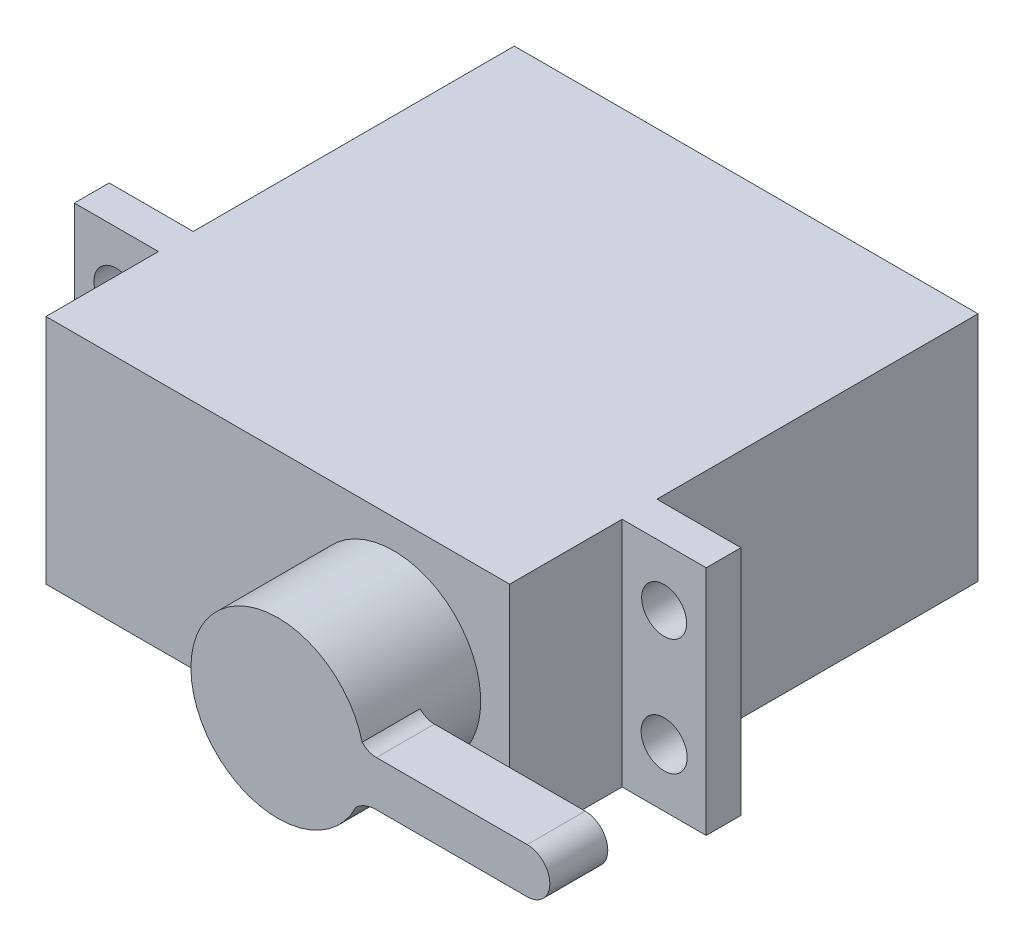
SolidWorks part; units mm, degrees
ref_plane "Front Plane" through (0, 0, 0) normal (0, 0, 1) x (1, 0, 0)
ref_plane "Top Plane" through (0, 0, 0) normal (0, 1, 0) x (1, 0, 0)
ref_plane "Right Plane" through (0, 0, 0) normal (1, 0, 0) x (0, 0, -1)
sketch "Sketch1" plane through (0, 0, 0) normal (0, 1, 0) x (1, 0, 0)
  line L1 (-27.6845, 15.2601) -> (12.3155, 15.2601)
  line L2 (-27.6845, 15.2601) -> (-27.6845, -25.1399)
  line L3 (-27.6845, -25.1399) -> (12.3155, -25.1399)
  line L4 (12.3155, 15.2601) -> (12.3155, -25.1399)
  dimension "D1" = 40
  dimension "D2" = 40.4
extrude "Boss-Extrude1" add sketch "Sketch1" along normal blind 20
sketch "Sketch3" plane through (12.3155, 0, 0) normal (1, 0, 0) x (0, 0, -1)
  line L0 (-25.1399, 20) -> (15.2601, 20) construction
  line L1 (-25.1399, 0) -> (15.2601, 0) construction
  line L2 (-15.4399, 20) -> (-12.4399, 20)
  line L3 (-15.4399, 20) -> (-15.4399, 0)
  line L4 (-15.4399, 0) -> (-12.4399, 0)
  line L5 (-12.4399, 20) -> (-12.4399, 0)
  line L7 (15.2601, 20) -> (15.2601, 0) construction
  dimension "D1" = 27.7
  dimension "D2" = 3
extrude "Boss-Extrude2" add sketch "Sketch3" along normal blind 7.25
sketch "Sketch4" plane through (0, 0, 0) normal (0, -1, 0) x (-1, 0, 0)
  line L0 (7.6845, -25.1399) -> (7.6845, 15.2601) construction
  line L1 (27.6845, -25.1399) -> (-12.3155, -25.1399) construction
  line L2 (-12.3155, 15.2601) -> (27.6845, 15.2601) construction
ref_plane "Plane1" through (-7.6845, 0, 0) normal (-1, 0, 0) x (0, 0, 1)
mirror "Mirror1" about plane through (-7.6845, 0, 0) normal (-1, 0, 0) of "Boss-Extrude2"
sketch "Sketch5" plane through (0, 0, 15.4399) normal (0, 0, 1) x (1, 0, 0)
  line L1 (19.5655, 0) -> (12.3155, 0) construction
  circle A0 centre (15.9405, 15) radius 1.9389
  circle A1 centre (15.9405, 5) radius 1.9865
  dimension "D1" = 10
  dimension "D3" = 5
extrude "Cut-Extrude1" cut sketch "Sketch5" against normal blind 7.25
mirror "Mirror2" about plane through (-7.6845, 0, 0) normal (-1, 0, 0) of "Cut-Extrude1"
sketch "Sketch6" plane through (0, 0, 25.1399) normal (0, 0, 1) x (1, 0, 0)
  line L0 (-27.6845, 20) -> (-27.6845, 0) construction
  circle A0 centre (2.3155, 10) radius 7.5
  dimension "D1" = 15
  dimension "D2" = 30
extrude "Boss-Extrude3" add sketch "Sketch6" along normal blind 10
sketch "Sketch8" plane through (0, 0, 35.1399) normal (0, 0, 1) x (1, 0, 0)
  line L0 (10.8185, 7.398) -> (23.8284, 7.398)
  line L1 (10.8185, 11.301) -> (23.8284, 11.301)
  arc A0 (23.8284, 11.301) -> (23.8284, 7.398) centre (23.8284, 9.3495) cw
  arc A1 (10.8185, 11.301) -> (9.1291, 13.1345) centre (10.8185, 12.996) cw
  circle A2 centre (2.3155, 10) radius 7.5 construction
  arc A4 (10.8185, 7.398) -> (9.061, 6.7215) centre (10.8185, 4.777) ccw
  circle A6 centre (2.3155, 10) radius 7.5
  arc A7 (9.1291, 13.1345) -> (9.061, 6.7215) centre (2.3155, 10) ccw
  dimension "D1" = 0
extrude "Boss-Extrude4" add sketch "Sketch8" against normal blind 5
